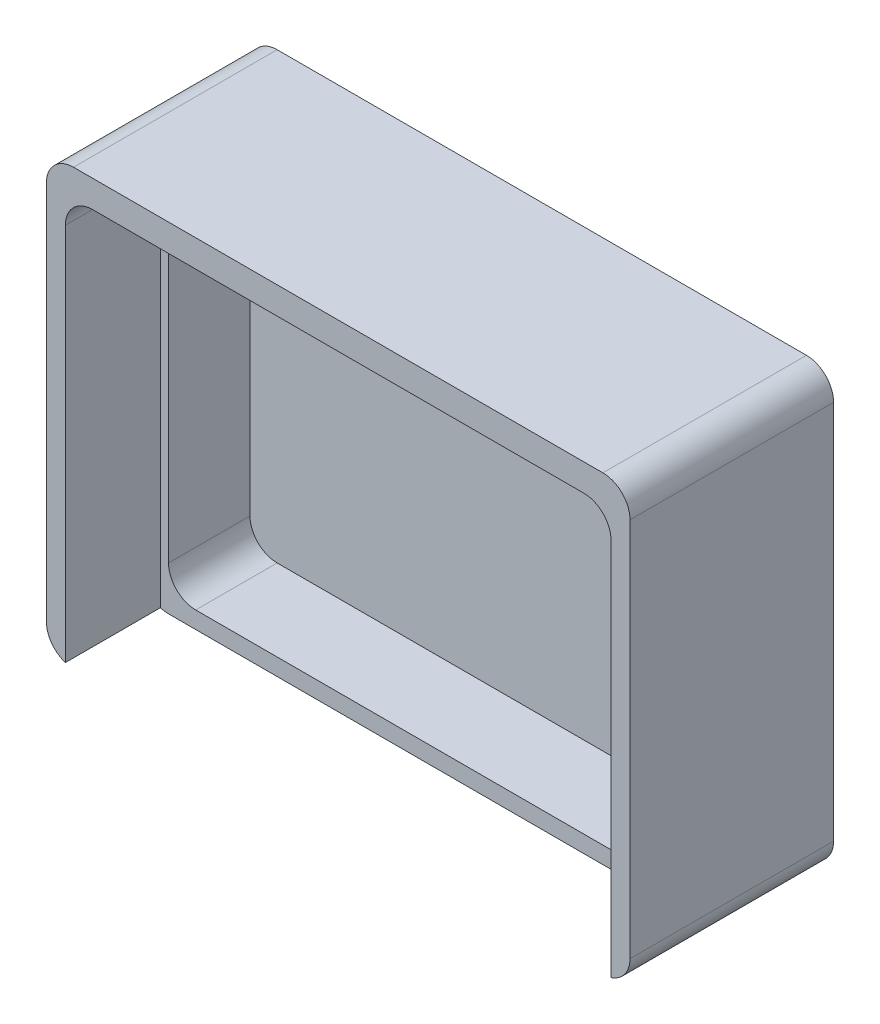
SolidWorks part; units mm, degrees
ref_plane "前视基准面" through (0, 0, 0) normal (0, 0, 1) x (1, 0, 0)
ref_plane "上视基准面" through (0, 0, 0) normal (0, 1, 0) x (1, 0, 0)
ref_plane "右视基准面" through (0, 0, 0) normal (1, 0, 0) x (0, 0, -1)
sketch "Sketch1" plane through (0, 0, 0) normal (0, 0, 1) x (1, 0, 0)
  line L0 (0, -16.875) -> (0, 15.125) construction
  line L1 (21.5, 15.125) -> (-21.5, -16.875) construction
  line L2 (-21.5, 15.125) -> (-21.5, -16.875)
  line L3 (-21.5, -16.875) -> (21.5, -16.875)
  line L4 (21.5, 15.125) -> (21.5, -16.875)
  line L5 (21.5, -16.875) -> (-21.5, 15.125) construction
  line L6 (21.5, 15.125) -> (-21.5, 15.125)
  point P0 (0, 0)
  dimension "D1" = 43
  dimension "D2" = 32
extrude "Boss-Extrude1" add sketch "Sketch1" along normal blind 15
sketch "Sketch2" plane through (0, 0, 15) normal (0, 0, 1) x (1, 0, 0)
  line L0 (0, -16.875) -> (0, -1.875) construction
  line L1 (-21.5, -16.875) -> (21.5, -16.875) construction
  line L3 (-20.1, 13.125) -> (20.1, 13.125)
  line L4 (-20.1, 13.125) -> (-20.1, -16.875)
  line L5 (-20.1, -16.875) -> (20.1, -16.875)
  line L6 (20.1, 13.125) -> (20.1, -16.875)
  line L7 (-20.1, 13.125) -> (20.1, -16.875) construction
  line L8 (-20.1, -16.875) -> (20.1, 13.125) construction
  dimension "D1" = 15
  dimension "D2" = 40.2
  dimension "D3" = 30
extrude "Cut-Extrude1" cut sketch "Sketch2" against normal blind 7
sketch "Sketch3" plane through (0, 0, 8) normal (0, 0, 1) x (1, 0, 0)
  line L0 (0, -16.875) -> (0, -1.625) construction
  line L1 (-20.1, -16.875) -> (20.1, -16.875) construction
  line L3 (-19.5, 12.375) -> (19.5, 12.375)
  line L4 (-19.5, 12.375) -> (-19.5, -15.625)
  line L5 (-19.5, -15.625) -> (19.5, -15.625)
  line L6 (19.5, 12.375) -> (19.5, -15.625)
  line L7 (-19.5, 12.375) -> (19.5, -15.625) construction
  line L8 (-19.5, -15.625) -> (19.5, 12.375) construction
  dimension "D1" = 15.25
  dimension "D2" = 39
  dimension "D3" = 28
extrude "Cut-Extrude2" cut sketch "Sketch3" against normal blind 6
fillet "Fillet2" radius 2 6 edges at (19.5, 12.375, 5) (-19.5, 12.375, 5) (20.1, 13.125, 11.5) (-20.1, 13.125, 11.5) (19.5, -15.625, 5) (-19.5, -15.625, 5)
fillet "Fillet4" radius 2 4 edges at (-21.5, -16.875, 7.5) (21.5, -16.875, 7.5) (21.5, 15.125, 7.5) (-21.5, 15.125, 7.5)
